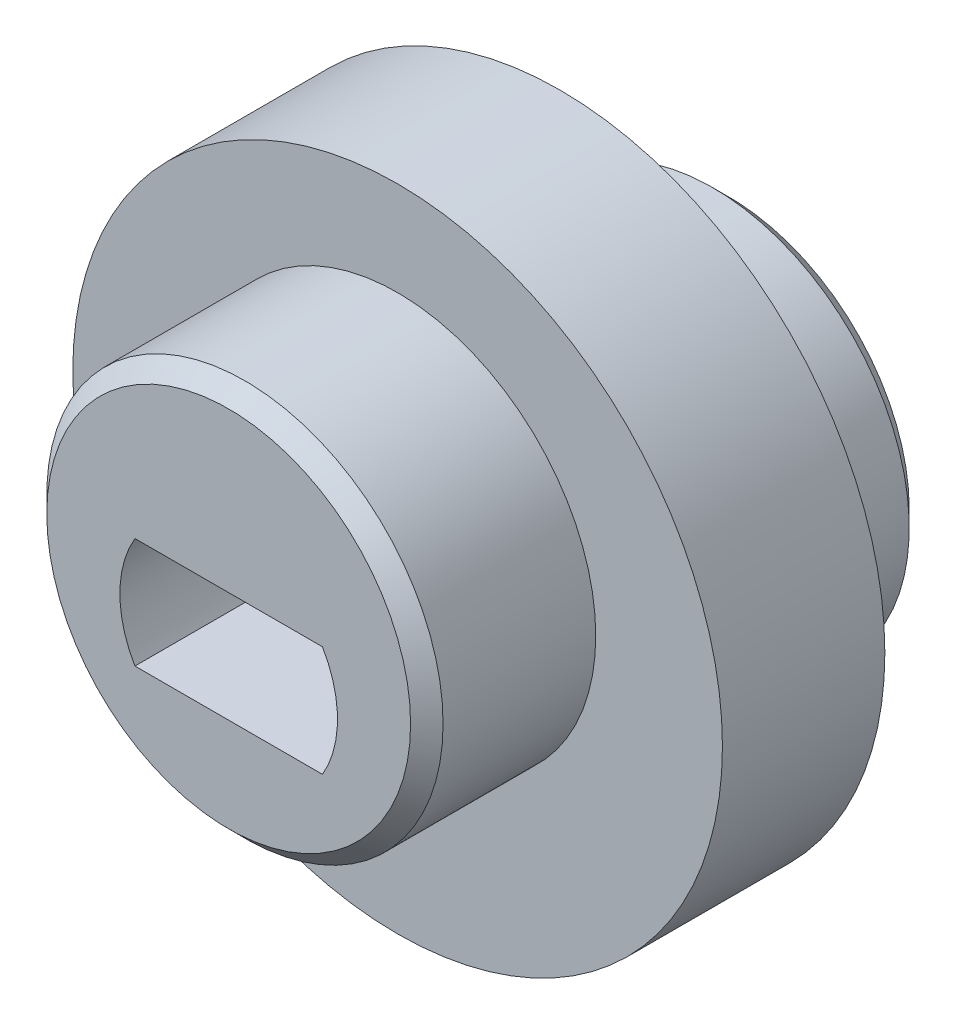
SolidWorks part; units mm, degrees
material "Polylactic Acid (PLA)"
ref_plane "Front Plane" through (0, 0, 0) normal (0, 0, 1) x (1, 0, 0)
ref_plane "Top Plane" through (0, 0, 0) normal (0, 1, 0) x (1, 0, 0)
ref_plane "Right Plane" through (0, 0, 0) normal (1, 0, 0) x (0, 0, -1)
sketch "Sketch6" plane through (0, 0, 0) normal (0, 0, 1) x (1, 0, 0)
  circle A0 centre (0, 0) radius 6
  dimension "D1" = 12
extrude "Boss-Extrude4" add sketch "Sketch6" along normal mid plane 5
sketch "Sketch7" plane through (0, 0, 2.5) normal (0, 0, 1) x (1, 0, 0)
  circle A0 centre (0, 1) radius 6.1
  dimension "D1" = 12.2
  dimension "D2" = 1
extrude "Boss-Extrude5" add sketch "Sketch7" along normal blind 5.2
sketch "Sketch8" plane through (0, 0, -2.5) normal (0, 0, -1) x (-1, 0, 0)
  circle A0 centre (0, -1) radius 6.05
  dimension "D1" = 12.1
  dimension "D2" = 1
extrude "Boss-Extrude6" add sketch "Sketch8" along normal blind 5.2
sketch "Sketch13" plane through (0, 0, 2.5) normal (0, 0, 1) x (1, 0, 0)
  circle A2 centre (0, 0) radius 10
  dimension "D1" = 20
extrude "Boss-Extrude7" add sketch "Sketch13" against normal up to surface (5 mm away) up to face at (0, 5.525, -2.5)
sketch "Sketch11" plane through (0, 0, 2.5) normal (0, 0, 1) x (1, 0, 0)
  line L0 (-2.8866, -1.7) -> (2.8866, -1.7)
  line L1 (-2.7699, -1.5) -> (2.7699, -1.5) construction
  line L2 (-2.7699, -1.5) -> (-2.7699, 1.5) construction
  line L3 (-2.7699, 1.5) -> (2.7699, 1.5) construction
  line L4 (2.7699, -1.5) -> (2.7699, 1.5) construction
  line L5 (-2.7699, -1.5) -> (2.7699, 1.5) construction
  line L6 (-2.7699, 1.5) -> (2.7699, -1.5) construction
  line L7 (-2.8866, 1.7) -> (2.8866, 1.7)
  arc A0 (-2.7699, 1.5) -> (-2.7699, -1.5) centre (0, 0) ccw construction
  arc A1 (2.7699, -1.5) -> (2.7699, 1.5) centre (0, 0) ccw construction
  arc A2 (2.8866, -1.7) -> (2.8866, 1.7) centre (0, 0) ccw
  arc A3 (-2.8866, 1.7) -> (-2.8866, -1.7) centre (0, 0) ccw
  dimension "D1" = 6.3
  dimension "D2" = 1.5
  dimension "D3" = 0.2
extrude "Cut-Extrude1" cut sketch "Sketch11" against normal through all both and the other way through all
chamfer "Chamfer1" distance 0.5 angle 45 2 edges at (-6.05, -1, -7.7) (6.1, 1, 7.7)
